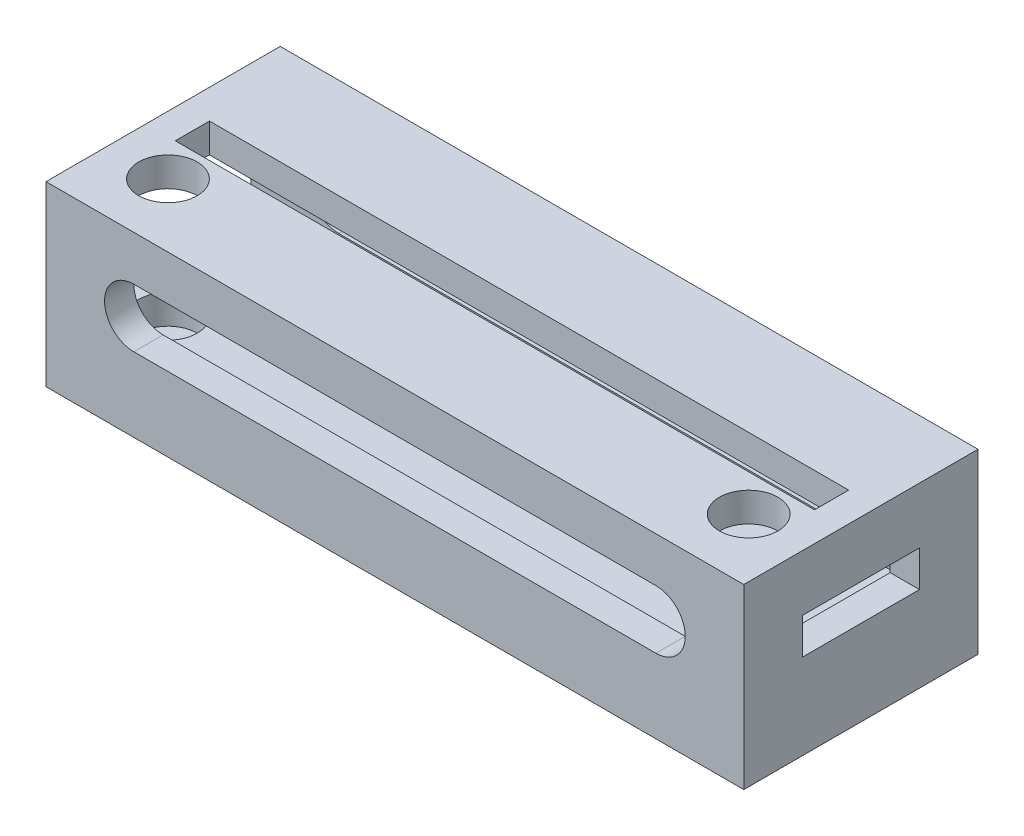
SolidWorks part; units mm, degrees
ref_plane "Front Plane" through (0, 0, 0) normal (0, 0, 1) x (1, 0, 0)
ref_plane "Top Plane" through (0, 0, 0) normal (0, 1, 0) x (1, 0, 0)
ref_plane "Right Plane" through (0, 0, 0) normal (1, 0, 0) x (0, 0, -1)
sketch "Sketch1" plane through (0, 0, 0) normal (0, 1, 0) x (1, 0, 0)
  line L1 (-32.75, -4.5) -> (32.75, -4.5)
  line L2 (-32.75, -4.5) -> (-32.75, 4.5)
  line L3 (-32.75, 4.5) -> (32.75, 4.5)
  line L4 (32.75, -4.5) -> (32.75, 4.5)
  line L5 (-32.75, -4.5) -> (32.75, 4.5) construction
  line L6 (-32.75, 4.5) -> (32.75, -4.5) construction
  circle A0 centre (-29.75, 0) radius 0.9984
  circle A1 centre (29.75, 0) radius 1.2431
  point P0 (0, 0)
  dimension "D1" = 9
  dimension "D2" = 65.5
  dimension "D3" = 29.75
  dimension "D4" = 59.5
extrude "Boss-Extrude1" add sketch "Sketch1" along normal blind 6
sketch "Sketch3" plane through (0, 0, -4.5) normal (0, 0, -1) x (-1, 0, 0)
  line L1 (-32.75, 6) -> (32.75, 6)
  line L2 (-32.75, 6) -> (-32.75, 0)
  line L3 (-32.75, 0) -> (32.75, 0)
  line L4 (32.75, 6) -> (32.75, 0)
extrude "Boss-Extrude2" add sketch "Sketch3" along normal blind 10
sketch "Sketch4" plane through (0, 0, 4.5) normal (0, 0, 1) x (1, 0, 0)
  line L1 (-32.75, 6) -> (32.75, 6)
  line L2 (-32.75, 6) -> (-32.75, 0)
  line L3 (-32.75, 0) -> (32.75, 0)
  line L4 (32.75, 6) -> (32.75, 0)
extrude "Boss-Extrude3" add sketch "Sketch4" along normal blind 2
sketch "Sketch5" plane through (0, 6, 0) normal (0, 1, 0) x (1, 0, 0)
  line L5 (-32.75, 14.5) -> (-32.75, -6.5) construction
  line L6 (32.75, -6.5) -> (-32.75, -6.5)
  line L7 (32.75, -6.5) -> (32.75, -3.5)
  line L8 (32.75, -3.5) -> (-32.75, -3.5)
  line L9 (-32.75, -6.5) -> (-32.75, -3.5)
  dimension "D1" = 3
extrude "Boss-Extrude4" add sketch "Sketch5" along normal blind 9.2
sketch "Sketch7" plane through (-32.75, 0, 0) normal (-1, 0, 0) x (0, 0, 1)
  line L1 (6.5, 15.2) -> (-14.5, 15.2)
  line L2 (6.5, 15.2) -> (6.5, 0)
  line L3 (6.5, 0) -> (-14.5, 0)
  line L4 (-14.5, 15.2) -> (-14.5, 0)
extrude "Boss-Extrude6" add sketch "Sketch7" along normal blind 3
sketch "Sketch12" plane through (0, 0, -14.5) normal (0, 0, -1) x (-1, 0, 0)
  line L0 (-32.75, 15.2) -> (-32.75, 6) construction
  line L1 (-32.75, 15.2) -> (35.75, 15.2)
  line L2 (-32.75, 15.2) -> (-32.75, 0)
  line L3 (-32.75, 0) -> (35.75, 0)
  line L4 (35.75, 15.2) -> (35.75, 0)
  dimension "D1" = 0
extrude "Boss-Extrude10" add sketch "Sketch12" along normal blind 3
sketch "Sketch13" plane through (32.75, 0, 0) normal (1, 0, 0) x (0, 0, -1)
  line L0 (17.5, 15.2) -> (17.5, 0) construction
  line L1 (-6.5, 15.2) -> (17.5, 15.2)
  line L2 (-6.5, 15.2) -> (-6.5, 12.45)
  line L3 (-6.5, 12.45) -> (17.5, 12.45)
  line L4 (17.5, 15.2) -> (17.5, 12.45)
  line L5 (-3.5, 15.2) -> (-3.5, 6) construction
  line L6 (17.5, 8.75) -> (-6.5, 8.75)
  line L7 (17.5, 8.75) -> (17.5, 0)
  line L8 (17.5, 0) -> (-6.5, 0)
  line L9 (-6.5, 8.75) -> (-6.5, 0)
  line L10 (-6.5, 15.2) -> (-0.5, 15.2)
  line L11 (-6.5, 15.2) -> (-6.5, 8.75)
  line L12 (-6.5, 8.75) -> (-0.5, 8.75)
  line L13 (-0.5, 15.2) -> (-0.5, 8.75)
  line L14 (17.5, 15.2) -> (11.5, 15.2)
  line L15 (17.5, 15.2) -> (17.5, 8.75)
  line L16 (17.5, 8.75) -> (11.5, 8.75)
  line L17 (11.5, 15.2) -> (11.5, 8.75)
  line L18 (14.5, 15.2) -> (14.5, 6) construction
  line L19 (-3.5, 6) -> (14.5, 6) construction
  dimension "D1" = 3
  dimension "D2" = 3
  dimension "D3" = 2.75
  dimension "D4" = 2.75
extrude "Boss-Extrude11" add sketch "Sketch13" along normal blind 3
sketch "Sketch6" plane through (0, 0, 6.5) normal (0, 0, 1) x (1, 0, 0)
  line L5 (-26.75, 13.6) -> (26.75, 13.6)
  line L6 (26.75, 13.6) -> (26.75, 7.6)
  line L7 (26.75, 7.6) -> (-26.75, 7.6)
  line L8 (-26.75, 7.6) -> (-26.75, 13.6)
  line L12 (-35.75, 0) -> (-35.75, 15.2) construction
  line L14 (35.75, 15.2) -> (35.75, 0) construction
  circle A0 centre (-26.75, 10.6) radius 3
  circle A1 centre (26.75, 10.6) radius 3
  dimension "D1" = 6
  dimension "D4" = 6
  dimension "D2" = 9
  dimension "D5" = 9
extrude "Cut-Extrude2" cut sketch "Sketch6" against normal through all contours L8 A0 | L8 A0 | L6 A1 | L6 A1 | A1 L5 A0 L7
sketch "Sketch11" plane through (-35.75, 0, 0) normal (-1, 0, 0) x (0, 0, 1)
  line L0 (6.5, 0) -> (6.5, 15.2) construction
  line L1 (-14.5, 15.2) -> (3.5, 15.2)
  line L2 (-14.5, 15.2) -> (-14.5, 6)
  line L3 (-14.5, 6) -> (3.5, 6)
  line L4 (3.5, 15.2) -> (3.5, 6)
  line L6 (-17.5, 0) -> (6.5, 0) construction
  line L8 (-17.5, 0) -> (-17.5, 15.2) construction
  dimension "D1" = 3
  dimension "D3" = 6
  dimension "D4" = 3
extrude "Cut-Extrude4" cut sketch "Sketch11" against normal blind 3
sketch "Sketch14" plane through (0, 15.2, 0) normal (0, 1, 0) x (1, 0, 0)
  line L1 (-35.75, 17.5) -> (35.75, 17.5)
  line L2 (-35.75, 17.5) -> (-35.75, -6.5)
  line L3 (-35.75, -6.5) -> (35.75, -6.5)
  line L4 (35.75, 17.5) -> (35.75, -6.5)
extrude "Boss-Extrude12" add sketch "Sketch14" along normal blind 3
sketch "Sketch15" plane through (0, 18.2, 0) normal (0, 1, 0) x (1, 0, 0)
  line L0 (35.75, -6.5) -> (35.75, 17.5) construction
  line L1 (-32.75, 7.25) -> (32.75, 7.25)
  line L2 (-32.75, 7.25) -> (-32.75, 3.75)
  line L3 (-32.75, 3.75) -> (32.75, 3.75)
  line L4 (32.75, 7.25) -> (32.75, 3.75)
  line L5 (-35.75, 17.5) -> (-35.75, -6.5) construction
  line L6 (-35.75, -6.5) -> (35.75, -6.5) construction
  dimension "D1" = 3
  dimension "D2" = 3
  dimension "D3" = 10.25
  dimension "D4" = 3.5
extrude "Cut-Extrude5" cut sketch "Sketch15" against normal blind 3
sketch "Sketch16" plane through (0, 18.2, 0) normal (0, 1, 0) x (1, 0, 0)
  circle A2 centre (-29.75, 0) radius 3
  circle A3 centre (29.75, 0) radius 3
  dimension "D1" = 6
  dimension "D2" = 6
extrude "Cut-Extrude6" cut sketch "Sketch16" against normal offset from surface (15.2 mm away) 3 up to face at (29.75, 6, 1.2431) offset beyond the face yes
equation "\"D4@Sketch6\"= \"D1@Sketch6\""
